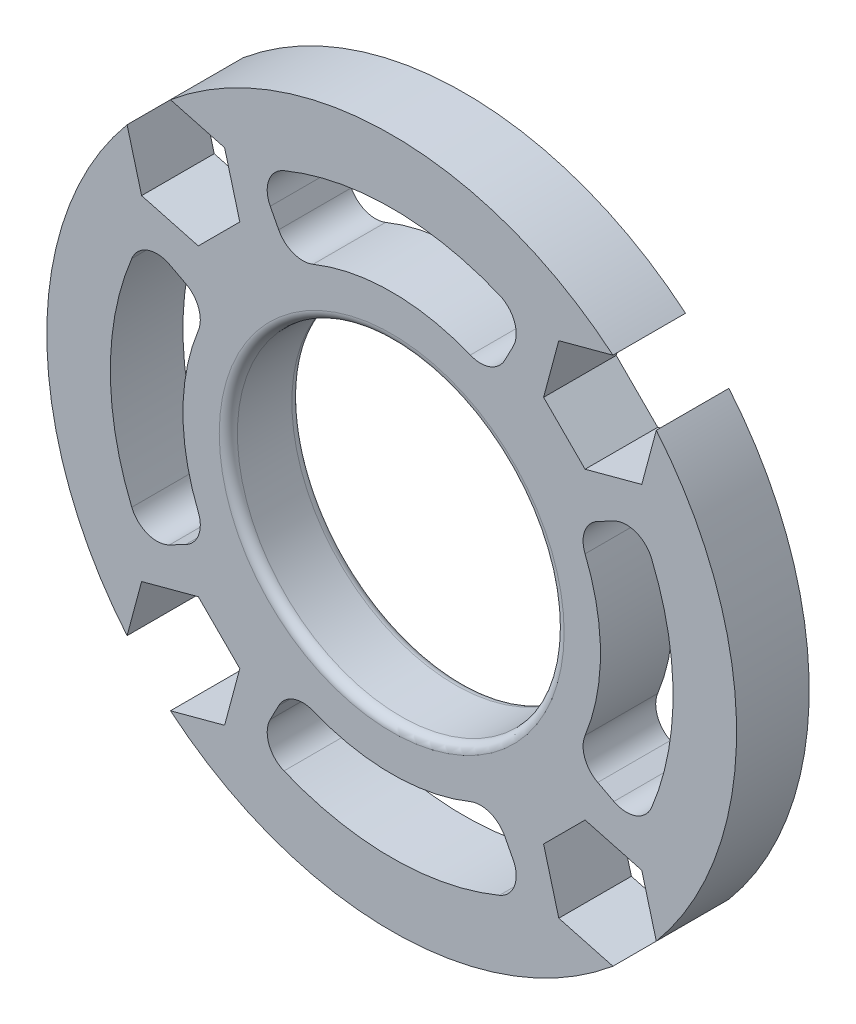
SolidWorks part; units mm, degrees
ref_plane "Front Plane" through (0, 0, 0) normal (0, 0, 1) x (1, 0, 0)
ref_plane "Top Plane" through (0, 0, 0) normal (0, 1, 0) x (1, 0, 0)
ref_plane "Right Plane" through (0, 0, 0) normal (1, 0, 0) x (0, 0, -1)
sketch "Sketch1" plane through (0, 0, 0) normal (0, 0, 1) x (1, 0, 0)
  line L0 (0, 0) -> (0, 19) construction
  line L1 (6.6897, 12.241) -> (6.226, 11.3504)
  line L2 (-6.6897, 12.241) -> (-6.226, 11.3504)
  line L3 (12.241, 6.6897) -> (11.3504, 6.226)
  line L4 (12.241, -6.6897) -> (11.3504, -6.226)
  line L5 (6.6897, -12.241) -> (6.226, -11.3504)
  line L6 (-6.6897, -12.241) -> (-6.226, -11.3504)
  line L7 (-12.241, -6.6897) -> (-11.3504, -6.226)
  line L8 (-12.241, 6.6897) -> (-11.3504, 6.226)
  circle A0 centre (0, 0) radius 19
  circle A1 centre (0, 0) radius 9
  arc A2 (4.3307, 10.6534) -> (-4.3307, 10.6534) centre (0, 0) ccw
  arc A3 (5.9334, 14.3194) -> (-5.9334, 14.3194) centre (0, 0) ccw
  arc A4 (6.6897, 12.241) -> (5.9334, 14.3194) centre (5.3592, 12.9336) ccw
  arc A5 (6.226, 11.3504) -> (4.3307, 10.6534) centre (4.8955, 12.043) cw
  arc A6 (-6.226, 11.3504) -> (-4.3307, 10.6534) centre (-4.8955, 12.043) ccw
  arc A7 (-6.6897, 12.241) -> (-5.9334, 14.3194) centre (-5.3592, 12.9336) cw
  arc A8 (10.6534, -4.3307) -> (10.6534, 4.3307) centre (0, 0) ccw
  arc A9 (11.3504, 6.226) -> (10.6534, 4.3307) centre (12.043, 4.8955) ccw
  arc A10 (12.241, 6.6897) -> (14.3194, 5.9334) centre (12.9336, 5.3592) cw
  arc A11 (14.3194, -5.9334) -> (14.3194, 5.9334) centre (0, 0) ccw
  arc A12 (12.241, -6.6897) -> (14.3194, -5.9334) centre (12.9336, -5.3592) ccw
  arc A13 (11.3504, -6.226) -> (10.6534, -4.3307) centre (12.043, -4.8955) cw
  arc A14 (-4.3307, -10.6534) -> (4.3307, -10.6534) centre (0, 0) ccw
  arc A15 (6.226, -11.3504) -> (4.3307, -10.6534) centre (4.8955, -12.043) ccw
  arc A16 (6.6897, -12.241) -> (5.9334, -14.3194) centre (5.3592, -12.9336) cw
  arc A17 (-5.9334, -14.3194) -> (5.9334, -14.3194) centre (0, 0) ccw
  arc A18 (-6.6897, -12.241) -> (-5.9334, -14.3194) centre (-5.3592, -12.9336) ccw
  arc A19 (-6.226, -11.3504) -> (-4.3307, -10.6534) centre (-4.8955, -12.043) cw
  arc A20 (-10.6534, 4.3307) -> (-10.6534, -4.3307) centre (0, 0) ccw
  arc A21 (-11.3504, -6.226) -> (-10.6534, -4.3307) centre (-12.043, -4.8955) ccw
  arc A22 (-12.241, -6.6897) -> (-14.3194, -5.9334) centre (-12.9336, -5.3592) cw
  arc A23 (-14.3194, 5.9334) -> (-14.3194, -5.9334) centre (0, 0) ccw
  arc A24 (-12.241, 6.6897) -> (-14.3194, 5.9334) centre (-12.9336, 5.3592) ccw
  arc A25 (-11.3504, 6.226) -> (-10.6534, 4.3307) centre (-12.043, 4.8955) cw
  point P56 (0, 0)
  dimension "D1" = 38
  dimension "D2" = 18
  dimension "D3" = 4
  dimension "D4" = 23
  dimension "D5" = 1.5
  dimension "D6" = 55
  dimension "D7" = 4
extrude "Boss-Extrude1" add sketch "Sketch1" along normal blind 4
sketch "Sketch2" plane through (0, 0, 0) normal (0, 0, -1) x (-1, 0, 0)
  line L0 (0, 0) -> (23.1637, 0) construction
  line L2 (19.8581, 19.8581) -> (0, 0) construction
  line L3 (10.6537, -8.3675) -> (8.3675, -10.6537)
  line L4 (13.7767, 9.2043) -> (14.6135, 12.3273)
  line L5 (14.6135, 12.3273) -> (12.3273, 14.6135)
  line L6 (12.3273, 14.6135) -> (9.2043, 13.7767)
  line L7 (9.2043, 13.7767) -> (8.3675, 10.6537)
  line L8 (8.3675, 10.6537) -> (10.6537, 8.3675)
  line L9 (10.6537, 8.3675) -> (13.7767, 9.2043)
  line L10 (8.3675, -10.6537) -> (9.2043, -13.7767)
  line L11 (9.2043, -13.7767) -> (12.3273, -14.6135)
  line L12 (12.3273, -14.6135) -> (14.6135, -12.3273)
  line L13 (14.6135, -12.3273) -> (13.7767, -9.2043)
  line L14 (13.7767, -9.2043) -> (10.6537, -8.3675)
  line L15 (-8.3675, -10.6537) -> (-10.6537, -8.3675)
  line L16 (-10.6537, -8.3675) -> (-13.7767, -9.2043)
  line L17 (-13.7767, -9.2043) -> (-14.6135, -12.3273)
  line L18 (-14.6135, -12.3273) -> (-12.3273, -14.6135)
  line L19 (-12.3273, -14.6135) -> (-9.2043, -13.7767)
  line L20 (-9.2043, -13.7767) -> (-8.3675, -10.6537)
  line L21 (-10.6537, 8.3675) -> (-8.3675, 10.6537)
  line L22 (-8.3675, 10.6537) -> (-9.2043, 13.7767)
  line L23 (-9.2043, 13.7767) -> (-12.3273, 14.6135)
  line L24 (-12.3273, 14.6135) -> (-14.6135, 12.3273)
  line L25 (-14.6135, 12.3273) -> (-13.7767, 9.2043)
  line L26 (-13.7767, 9.2043) -> (-10.6537, 8.3675)
  circle A0 centre (0, 0) radius 16.25 construction
  circle A1 centre (11.4905, 11.4905) radius 2.8 construction
  point P34 (0, 0)
  dimension "D2" = 32.5
  dimension "D1" = 45
  dimension "D3" = 5.6
  dimension "D4" = 4
extrude "Cut-Extrude1" cut sketch "Sketch2" against normal blind 4
fillet "Fillet1" radius 0.5 2 edges at (9, 0, 4) (9, 0, 0)
equation "\"D3@Sketch2\"=5.4+.2"
